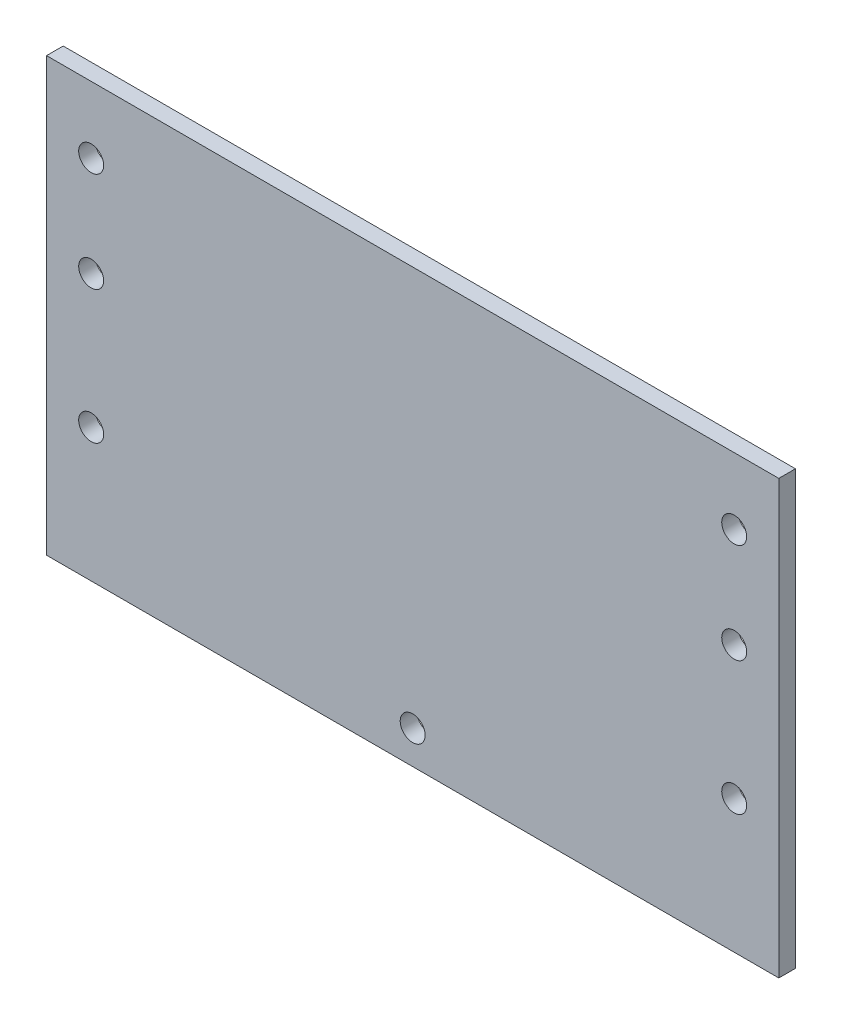
SolidWorks part; units mm, degrees
ref_plane "Front Plane" through (0, 0, 0) normal (0, 0, 1) x (1, 0, 0)
ref_plane "Top Plane" through (0, 0, 0) normal (0, 1, 0) x (1, 0, 0)
ref_plane "Right Plane" through (0, 0, 0) normal (1, 0, 0) x (0, 0, -1)
sketch "Sketch1" plane through (0, 0, 0) normal (0, 0, 1) x (1, 0, 0)
  line L1 (0, 0) -> (558.8, 0)
  line L2 (0, 0) -> (0, -330.2)
  line L3 (0, -330.2) -> (558.8, -330.2)
  line L4 (558.8, 0) -> (558.8, -330.2)
  dimension "D1" = 558.8
  dimension "D2" = 330.2
extrude "Boss-Extrude1" add sketch "Sketch1" along normal blind 12.7
sketch "Sketch4" plane through (0, 0, 0) normal (0, 0, -1) x (-1, 0, 0)
  line L0 (-279.4, 0) -> (-279.4, -330.2) construction
  line L1 (0, -330.2) -> (-558.8, -330.2) construction
  line L2 (-558.8, -330.2) -> (-558.8, 0) construction
  line L4 (-558.8, 0) -> (0, 0) construction
  circle A0 centre (-279.4, -304.8) radius 9.525
  circle A1 centre (-524.764, -228.6) radius 9.525
  circle A2 centre (-524.764, -127) radius 9.525
  circle A3 centre (-34.036, -228.6) radius 9.525
  circle A4 centre (-34.036, -127) radius 9.525
  circle A5 centre (-524.764, -50.8) radius 9.525
  circle A7 centre (-34.036, -50.8) radius 9.525
  dimension "D1" = 25.4
  dimension "D2" = 101.6
  dimension "D3" = 34.036
  dimension "D4" = 34.036
  dimension "D6" = 76.2
  dimension "D7" = 101.6
  dimension "D5" = 34.036
extrude "Cut-Extrude1" cut sketch "Sketch4" against normal blind 12.7
